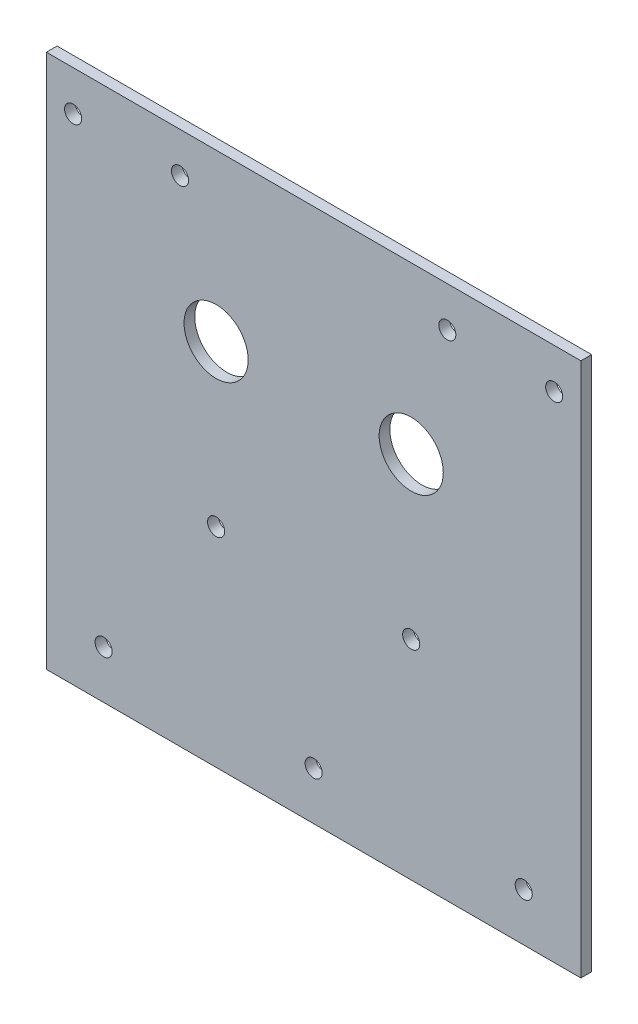
SolidWorks part; units mm, degrees
material "ｱｸﾘﾙ (中-上級の耐衝撃性)"
ref_plane "正面" through (0, 0, 0) normal (0, 0, 1) x (1, 0, 0)
ref_plane "平面" through (0, 0, 0) normal (0, 1, 0) x (1, 0, 0)
ref_plane "右側面" through (0, 0, 0) normal (1, 0, 0) x (0, 0, -1)
sketch "ｽｹｯﾁ1" plane through (0, 0, 0) normal (0, 0, 1) x (1, 0, 0)
  line L1 (-50, 50) -> (50, 50)
  line L2 (-50, 50) -> (-50, -50)
  line L3 (-50, -50) -> (50, -50)
  line L4 (50, 50) -> (50, -50)
  line L5 (-50, 50) -> (50, -50) construction
  line L6 (-50, -50) -> (50, 50) construction
  point P0 (0, 0)
  dimension "D1" = 100
  dimension "D2" = 100
extrude "ﾎﾞｽ - 押し出し1" add sketch "ｽｹｯﾁ1" along normal blind 2
sketch "ｽｹｯﾁ2" plane through (0, 0, 2) normal (0, 0, 1) x (1, 0, 0)
  line L0 (-50, 50) -> (-50, 42.5)
  line L1 (-50, 42.5) -> (-45, 42.5)
  line L2 (-45, 42.5) -> (-25, 42.5)
  line L3 (50, 50) -> (50, 42.5)
  line L4 (50, -50) -> (50, 50) construction
  line L5 (50, 42.5) -> (45, 42.5)
  line L6 (45, 42.5) -> (25, 42.5)
  circle A0 centre (-45, 42.5) radius 1.6
  circle A1 centre (-25, 42.5) radius 1.6
  circle A2 centre (25, 42.5) radius 1.6
  circle A3 centre (45, 42.5) radius 1.6
  dimension "D7" = 3.2
  dimension "D8" = 3.2
  dimension "D9" = 3.2
  dimension "D10" = 3.2
  dimension "D1" = 7.5
  dimension "D2" = 5
  dimension "D3" = 20
  dimension "D4" = 7.5
  dimension "D5" = 5
  dimension "D6" = 20
extrude "ｶｯﾄ - 押し出し1" cut sketch "ｽｹｯﾁ2" against normal blind 2
sketch "ｽｹｯﾁ3" plane through (0, 0, 2) normal (0, 0, 1) x (1, 0, 0)
  line L0 (0, -50) -> (0, -41)
  line L1 (-50, -50) -> (50, -50) construction
  circle A0 centre (0, -41) radius 1.6
  dimension "D2" = 3.2
  dimension "D1" = 9
extrude "ｶｯﾄ - 押し出し2" cut sketch "ｽｹｯﾁ3" against normal blind 10
sketch "ｽｹｯﾁ4" plane through (0, 0, 2) normal (0, 0, 1) x (1, 0, 0)
  line L0 (0, 50) -> (0, 19)
  line L1 (50, 50) -> (-50, 50) construction
  line L2 (0, 19) -> (18.25, 19)
  line L3 (0, 19) -> (-18.25, 19)
  circle A0 centre (-18.25, 19) radius 6
  circle A1 centre (18.25, 19) radius 6
  dimension "D4" = 12
  dimension "D5" = 12
  dimension "D1" = 31
  dimension "D2" = 18.25
  dimension "D3" = 18.25
extrude "ｶｯﾄ - 押し出し3" cut sketch "ｽｹｯﾁ4" against normal blind 38.65
sketch "ｽｹｯﾁ5" plane through (0, 0, 2) normal (0, 0, 1) x (1, 0, 0)
  line L0 (0, 50) -> (18.25, 50)
  line L1 (50, 50) -> (-50, 50) construction
  line L2 (18.25, 50) -> (18.25, -11)
  line L3 (0, 50) -> (-18.25, 50)
  line L4 (-18.25, 50) -> (-18.25, -11)
  circle A0 centre (-18.25, -11) radius 1.6
  circle A1 centre (18.25, -11) radius 1.6
  dimension "D5" = 3.2
  dimension "D6" = 3.2
  dimension "D1" = 18.25
  dimension "D2" = 61
  dimension "D3" = 18.25
  dimension "D4" = 61
extrude "ｶｯﾄ - 押し出し4" cut sketch "ｽｹｯﾁ5" against normal blind 38.6
sketch "ｽｹｯﾁ6" plane through (0, 0, 2) normal (0, 0, 1) x (1, 0, 0)
  line L0 (0, -41) -> (39.3, -41)
  line L1 (0, -41) -> (-39.3, -41)
  circle A0 centre (-39.3, -41) radius 1.6
  circle A1 centre (39.3, -41) radius 1.6
  dimension "D3" = 3.2
  dimension "D4" = 3.2
  dimension "D1" = 39.3
  dimension "D2" = 39.3
extrude "ｶｯﾄ - 押し出し5" cut sketch "ｽｹｯﾁ6" against normal blind 10
